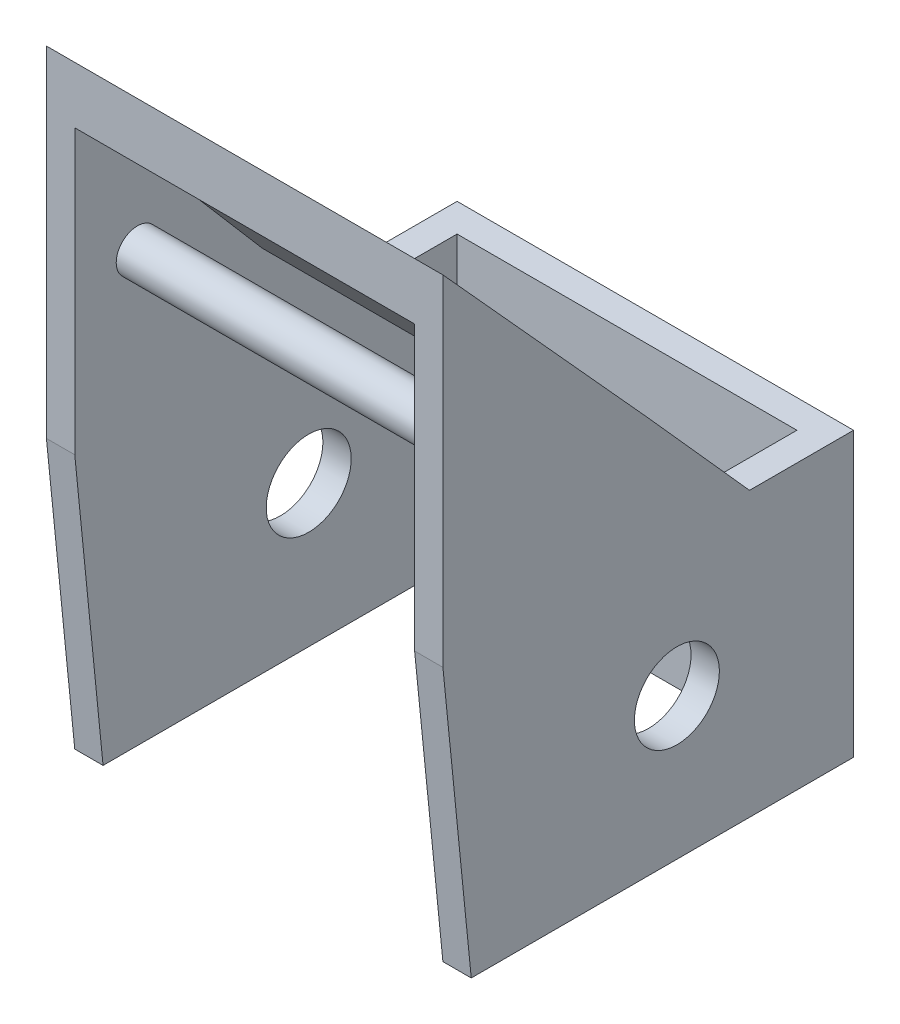
SolidWorks part; units mm, degrees
ref_plane "Front Plane" through (0, 0, 0) normal (0, 0, 1) x (1, 0, 0)
ref_plane "Top Plane" through (0, 0, 0) normal (0, 1, 0) x (1, 0, 0)
ref_plane "Right Plane" through (0, 0, 0) normal (1, 0, 0) x (0, 0, -1)
sketch "Sketch1" plane through (0, 0, 0) normal (0, 0, 1) x (1, 0, 0)
  line L1 (-70, 50) -> (70, 50)
  line L2 (-70, 50) -> (-70, -50)
  line L3 (-70, -50) -> (70, -50)
  line L4 (70, 50) -> (70, -50)
  line L5 (-70, 50) -> (70, -50) construction
  line L6 (-70, -50) -> (70, 50) construction
  point P0 (0, 0)
  dimension "D1" = 140
  dimension "D2" = 100
extrude "Boss-Extrude1" add sketch "Sketch1" along normal blind 10
sketch "Sketch2" plane through (0, 0, 10) normal (0, 0, 1) x (1, 0, 0)
  line L0 (70, 0) -> (-70, 0) construction
  line L1 (70, -50) -> (70, 50) construction
  line L2 (-70, 50) -> (-70, -50) construction
  line L3 (-70, -50) -> (70, -50) construction
  line L4 (70, 50) -> (60, 50)
  line L5 (70, 50) -> (70, -50)
  line L6 (70, -50) -> (60, -50)
  line L7 (60, 50) -> (60, -50)
  line L8 (70, 50) -> (-70, 50) construction
  line L9 (-70, 50) -> (-60, 50)
  line L10 (-70, 50) -> (-70, -50)
  line L11 (-70, -50) -> (-60, -50)
  line L12 (-60, 50) -> (-60, -50)
  dimension "D1" = 10
  dimension "D2" = 10
extrude "Boss-Extrude2" add sketch "Sketch2" along normal blind 120
sketch "Sketch3" plane through (-70, 0, 0) normal (-1, 0, 0) x (0, 0, 1)
  line L0 (130, 50) -> (145, 50)
  line L1 (145, 50) -> (135, -50)
  line L2 (135, -50) -> (130, -50)
  line L3 (130, 50) -> (130, -50)
  dimension "D1" = 15
  dimension "D2" = 5
extrude "Boss-Extrude3" add sketch "Sketch3" against normal blind 10
sketch "Sketch4" plane through (70, 0, 0) normal (1, 0, 0) x (0, 0, -1)
  line L0 (-130, 50) -> (-145, 50)
  line L1 (-145, 50) -> (-135, -50)
  line L2 (-135, -50) -> (-130, -50)
  line L3 (-130, -50) -> (-130, 50)
extrude "Boss-Extrude4" add sketch "Sketch4" against normal blind 10
sketch "Sketch6" plane through (-70, 0, 0) normal (-1, 0, 0) x (0, 0, 1)
  line L1 (145, 50) -> (0, 50) construction
  line L2 (72.5, 90) -> (145, 170)
  line L3 (145, 170) -> (145, 50)
  line L4 (145, 50) -> (72.5, 50)
  line L5 (72.5, 90) -> (36.7519, 50)
  line L6 (36.7519, 50) -> (72.5, 50)
  dimension "D1" = 40
  dimension "D2" = 120
extrude "Boss-Extrude6" add sketch "Sketch6" against normal blind 140
sketch "Sketch7" plane through (0, 50, 0) normal (0, -1, 0) x (1, 0, 0)
  line L0 (60, 145) -> (60, 36.7519) construction
  line L1 (-60, 145) -> (60, 145)
  line L2 (-60, 145) -> (-60, 46.499)
  line L3 (-60, 46.499) -> (60, 46.499)
  line L4 (60, 145) -> (60, 46.499)
extrude "Cut-Extrude1" cut sketch "Sketch7" against normal blind 30
sketch "Sketch8" plane through (-70, 0, 0) normal (-1, 0, 0) x (0, 0, 1)
  line L0 (0, 0) -> (68.901, 0) construction
  circle A0 centre (62.3874, 0) radius 15
  point P5 (29.1362, 0)
  point P6 (62.3874, 0)
  point P7 (44.1362, 0)
  point P8 (0, 0)
  point P9 (0, 0)
  point P10 (68.901, 0)
  point P11 (0, 0)
  dimension "D1" = 30
extrude "Cut-Extrude2" cut sketch "Sketch8" against normal blind 170
sketch "Sketch9" plane through (0, 0, 10) normal (0, 0, 1) x (1, 0, 0)
  circle A0 centre (0, 0) radius 15
  dimension "D1" = 30
extrude "Cut-Extrude3" cut sketch "Sketch9" against normal blind 170
sketch "Sketch13" plane through (-70, 0, 0) normal (-1, 0, 0) x (0, 0, 1)
  line L0 (36.7519, 50) -> (147.459, 50) construction
  line L1 (54.626, 70) -> (145, 70) construction
  line L2 (72.5, 90) -> (36.7519, 50) construction
  line L3 (145, 50) -> (145, 170) construction
  line L4 (70.1575, 70) -> (136.0395, 146.8178) construction
  line L5 (136.0395, 146.8178) -> (136.0395, 70) construction
  line L6 (70.1575, 70) -> (136.0395, 146.8178)
  line L7 (136.0395, 146.8178) -> (136.0395, 70)
  line L8 (136.0395, 70) -> (70.1575, 70)
extrude "Cut-Extrude4" cut sketch "Sketch13" against normal blind 140
sketch "Sketch14" plane through (0, 0, 145) normal (0, 0, 1) x (1, 0, 0)
  line L1 (-60, 80) -> (60, 80)
  line L2 (-60, 80) -> (-60, 150)
  line L3 (-60, 150) -> (60, 150)
  line L4 (60, 80) -> (60, 150)
  dimension "D1" = 120
  dimension "D2" = 70
extrude "Cut-Extrude5" cut sketch "Sketch14" against normal blind 10
sketch "Sketch15" plane through (-70, 0, 0) normal (-1, 0, 0) x (0, 0, 1)
  line L0 (136.0395, 146.8178) -> (136.0395, 70)
  line L1 (136.0395, 70) -> (70.1575, 70)
  line L2 (70.1575, 70) -> (136.0395, 146.8178)
extrude "Boss-Extrude8" add sketch "Sketch15" against normal blind 10
sketch "Sketch16" plane through (70, 0, 0) normal (1, 0, 0) x (0, 0, -1)
  line L0 (-136.0395, 146.8178) -> (-136.0395, 70)
  line L1 (-136.0395, 70) -> (-70.1575, 70)
  line L2 (-70.1575, 70) -> (-136.0395, 146.8178)
extrude "Boss-Extrude9" add sketch "Sketch16" against normal blind 10
sketch "Sketch17" plane through (60, 0, 0) normal (-1, 0, 0) x (0, 0, 1)
  circle A0 centre (122.8631, 101.4324) radius 7.5
  dimension "D1" = 15
extrude "Boss-Extrude10" add sketch "Sketch17" along normal blind 120
